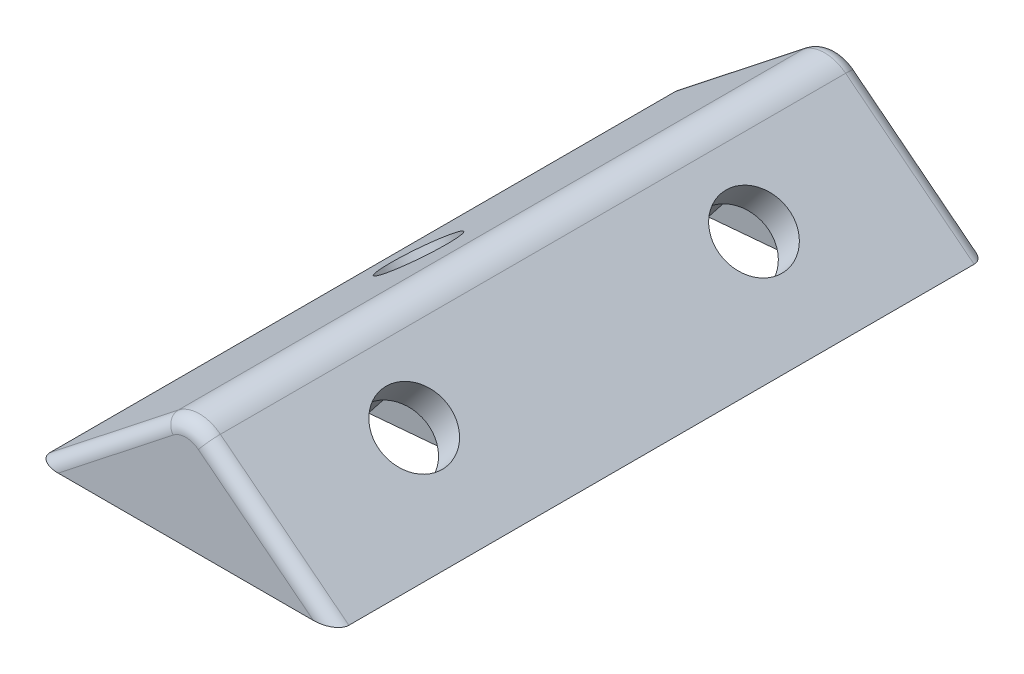
SolidWorks part; units mm, degrees
ref_plane "Front Plane" through (0, 0, 0) normal (0, 0, 1) x (1, 0, 0)
ref_plane "Top Plane" through (0, 0, 0) normal (0, 1, 0) x (1, 0, 0)
ref_plane "Right Plane" through (0, 0, 0) normal (1, 0, 0) x (0, 0, -1)
sketch "Sketch2" plane through (0, 0, 0) normal (0, 0, 1) x (1, 0, 0)
  line L1 (0, 2.3094) -> (-11, -6.3509)
  line L2 (-11, -6.3509) -> (11, -6.3509)
  line L3 (11, -6.3509) -> (0, 2.3094)
  dimension "D1" = 22
  dimension "D2" = 14
  dimension "D3" = 14
extrude "Boss-Extrude3" add sketch "Sketch2" along normal blind 48
sketch "Sketch4" plane through (-1.1224, 1.4257, 0) normal (-0.6186, 0.7857, 0) x (0.7857, 0.6186, 0)
  line L0 (-7.3214, -24) -> (1.4286, -24) construction
  line L1 (1.4286, -48) -> (1.4286, 0) construction
  circle A0 centre (-7.3214, -24) radius 2.625
  dimension "D1" = 5.25
  dimension "D2" = 8.75
extrude "Cut-Extrude2" cut sketch "Sketch4" against normal through all
sketch "Sketch5" plane through (1.1224, 1.4257, 0) normal (0.6186, 0.7857, 0) x (0.7857, -0.6186, 0)
  line L0 (5.3214, -36.5) -> (5.3214, -11.5) construction
  line L1 (-1.4286, -24) -> (5.3214, -24) construction
  line L2 (-1.4286, -48) -> (-1.4286, 0) construction
  circle A0 centre (5.3214, -11.5) radius 2.625
  circle A1 centre (5.3214, -36.5) radius 2.625
  dimension "D1" = 5.25
  dimension "D2" = 5.25
  dimension "D3" = 25
  dimension "D4" = 6.75
extrude "Cut-Extrude3" cut sketch "Sketch5" against normal through all
fillet "Fillet2" radius 2.5 1 edges at (0, 2.3094, 24)
ref_plane "Plane1" through (-8.1564, -10.36, 0) normal (0.6186, 0.7857, 0) x (0.7857, -0.6186, 0)
sketch "Sketch6" plane through (-8.1564, -10.36, 0) normal (0.6186, 0.7857, 0) x (0.7857, -0.6186, 0)
  line L1 (7.1603, -7.2002) -> (2.5171, -7.7576)
  line L2 (2.5171, -7.7576) -> (0.6782, -12.0574)
  line L3 (0.6782, -12.0574) -> (3.4825, -15.7998)
  line L4 (3.4825, -15.7998) -> (8.1257, -15.2424)
  line L5 (8.1257, -15.2424) -> (9.9646, -10.9426)
  line L6 (9.9646, -10.9426) -> (7.1603, -7.2002)
  line L7 (7.1603, -32.2002) -> (2.5171, -32.7576)
  line L8 (2.5171, -32.7576) -> (0.6782, -37.0574)
  line L9 (0.6782, -37.0574) -> (3.4825, -40.7998)
  line L10 (3.4825, -40.7998) -> (8.1257, -40.2424)
  line L11 (8.1257, -40.2424) -> (9.9646, -35.9426)
  line L12 (9.9646, -35.9426) -> (7.1603, -32.2002)
  circle A0 centre (5.3214, -11.5) radius 4.05 construction
  circle A1 centre (5.3214, -36.5) radius 4.05 construction
  dimension "D1" = 8.1
  dimension "D2" = 8.1
extrude "Cut-Extrude4" cut sketch "Sketch6" along normal blind 12.5
ref_plane "Plane2" through (8.1564, -10.36, 0) normal (-0.6186, 0.7857, 0) x (0.7857, 0.6186, 0)
sketch "Sketch7" plane through (8.1564, -10.36, 0) normal (-0.6186, 0.7857, 0) x (0.7857, 0.6186, 0)
  line L0 (-0.5397, -48) -> (-0.5397, 0) construction
  line L1 (-7.3214, -19.3235) -> (-11.3714, -21.6617)
  line L2 (-11.3714, -21.6617) -> (-11.3714, -26.3383)
  line L3 (-11.3714, -26.3383) -> (-7.3214, -28.6765)
  line L4 (-7.3214, -28.6765) -> (-3.2714, -26.3383)
  line L5 (-3.2714, -26.3383) -> (-3.2714, -21.6617)
  line L6 (-3.2714, -21.6617) -> (-7.3214, -19.3235)
  circle A0 centre (-7.3214, -24) radius 4.05 construction
  dimension "D1" = 8.1
extrude "Cut-Extrude6" cut sketch "Sketch7" along normal blind 12.5
fillet "Fillet3" radius 1 3 edges at (-6.2732, -2.6295, 0) (0, 1.6276, 0) (6.2732, -2.6295, 0)
fillet "Fillet4" radius 1 3 edges at (-6.2732, -2.6295, 48) (0, 1.6276, 48) (6.2732, -2.6295, 48)
